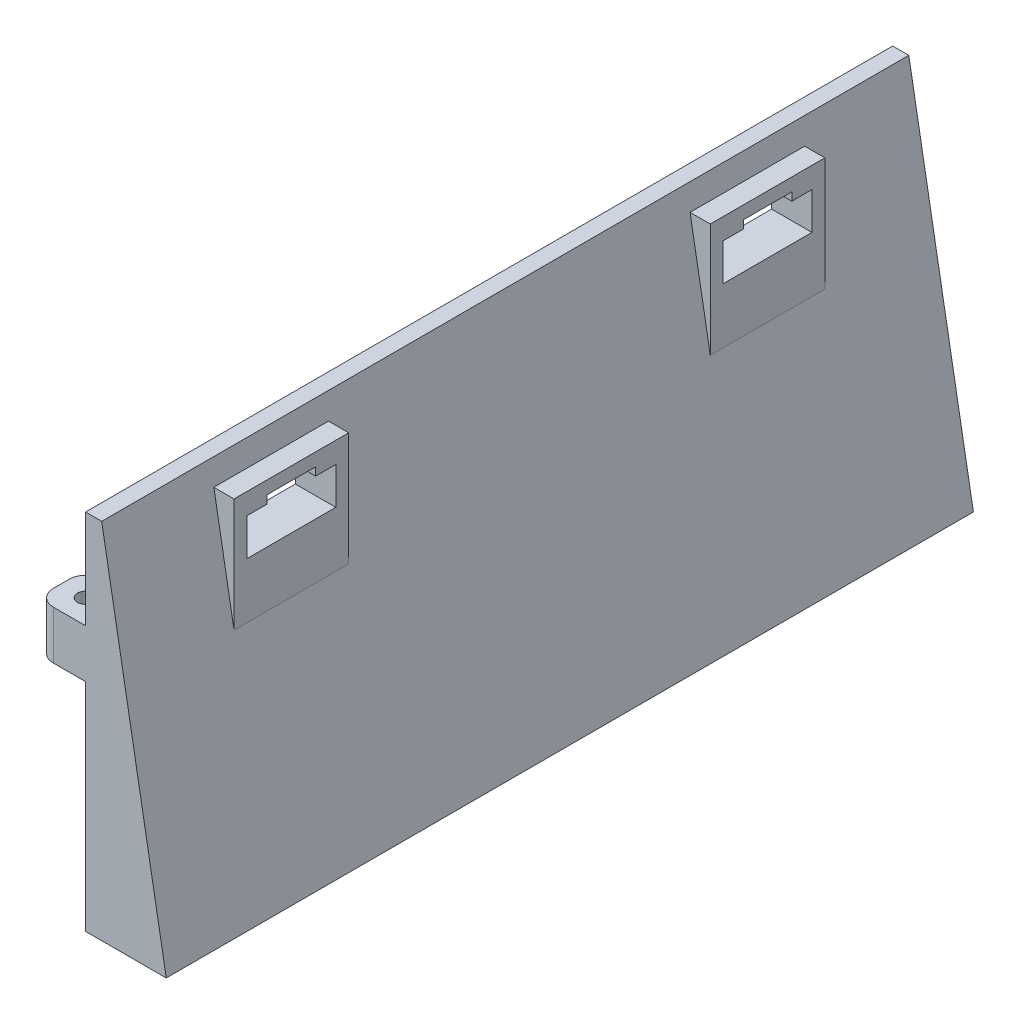
SolidWorks part; units mm, degrees
ref_plane "Front Plane" through (0, 0, 0) normal (0, 0, 1) x (1, 0, 0)
ref_plane "Top Plane" through (0, 0, 0) normal (0, 1, 0) x (1, 0, 0)
ref_plane "Right Plane" through (0, 0, 0) normal (1, 0, 0) x (0, 0, -1)
sketch "Sketch1" plane through (0, 0, 0) normal (0, 0, 1) x (1, 0, 0)
  line L0 (0, 0) -> (10, 0)
  line L1 (0, 0) -> (0, 45)
  line L2 (0, 45) -> (2, 45)
  line L3 (2, 45) -> (10, 0)
  dimension "D1" = 10
  dimension "D2" = 45
  dimension "D3" = 2
extrude "Boss-Extrude1" add sketch "Sketch1" along normal blind 100
sketch "Sketch3" plane through (0, 0, 0) normal (-1, 0, 0) x (0, 0, 1)
  line L0 (12.5, 0) -> (0, 0) construction
  line L1 (100, 0) -> (0, 0) construction
  line L2 (87.5, 0) -> (100, 0) construction
  line L3 (12.5, 0) -> (12.5, 7.1) construction
  line L4 (12.5, 7.1) -> (18.5, 7.1)
  line L5 (12.5, 7.1) -> (12.5, 13.1)
  line L6 (12.5, 13.1) -> (18.5, 13.1)
  line L7 (18.5, 13.1) -> (18.5, 7.1)
  line L8 (87.5, 0) -> (87.5, 7.1) construction
  line L9 (87.5, 7.1) -> (81.5, 7.1)
  line L10 (87.5, 7.1) -> (87.5, 13.1)
  line L11 (87.5, 13.1) -> (81.5, 13.1)
  line L12 (81.5, 13.1) -> (81.5, 7.1)
  line L13 (12.5, 7.1) -> (12.5, 13.1) construction
  dimension "D2" = 12.5
  dimension "D3" = 7.1
  dimension "D4" = 6
  dimension "D5" = 6
  dimension "D6" = 7.1
  dimension "D7" = 6
  dimension "D8" = 6
  dimension "D15" = 12.5
extrude "Boss-Extrude2" add sketch "Sketch3" along normal blind 6
sketch "Sketch4" plane through (0, 13.1, 0) normal (0, 1, 0) x (1, 0, 0)
  line L0 (-6, -84.5) -> (-3, -84.5) construction
  line L1 (-6, -87.5) -> (-6, -81.5) construction
  circle A0 centre (-3, -84.5) radius 1
  dimension "D2" = 2
  dimension "D1" = 3
extrude "Cut-Extrude2" cut sketch "Sketch4" against normal blind 10
sketch "Sketch5" plane through (0, 13.1, 0) normal (0, 1, 0) x (1, 0, 0)
  line L0 (-6, -15.5) -> (-3, -15.5) construction
  line L1 (-6, -18.5) -> (-6, -12.5) construction
  circle A0 centre (-3, -15.5) radius 1
  dimension "D2" = 2
  dimension "D1" = 3
extrude "Cut-Extrude3" cut sketch "Sketch5" against normal blind 10
fillet "Fillet1" radius 1 4 edges at (0, 10.1, 81.5) (0, 10.1, 87.5) (0, 10.1, 12.5) (0, 10.1, 18.5)
fillet "Fillet2" radius 2 4 edges at (-6, 10.1, 87.5) (-6, 10.1, 81.5) (-6, 10.1, 18.5) (-6, 10.1, 12.5)
sketch "Sketch7" plane through (0, 0, 0) normal (-1, 0, 0) x (0, 0, 1)
  line L0 (0, 45) -> (0, 40.6) construction
  line L1 (0, 45) -> (0, 0) construction
  line L2 (0, 40.6) -> (100, 40.6) construction
  line L3 (100, 45) -> (100, 0) construction
  line L4 (0, 40.6) -> (15, 40.6) construction
  line L5 (100, 40.6) -> (85, 40.6) construction
  line L6 (0, 40.6) -> (0, 35) construction
  line L7 (0, 35) -> (100, 35) construction
  line L8 (15, 40.6) -> (26, 40.6) construction
  line L9 (85, 40.6) -> (74, 40.6) construction
  line L10 (15, 40.6) -> (15, 35)
  line L11 (15, 35) -> (26, 35)
  line L12 (26, 35) -> (26, 40.6)
  line L13 (26, 40.6) -> (15, 40.6)
  line L14 (74, 40.6) -> (74, 35)
  line L15 (74, 35) -> (85, 35)
  line L16 (85, 35) -> (85, 40.6)
  line L17 (85, 40.6) -> (74, 40.6)
  dimension "D1" = 4.4
  dimension "D2" = 15
  dimension "D3" = 15
  dimension "D4" = 5.6
  dimension "D5" = 11
  dimension "D6" = 11
extrude "Cut-Extrude4" cut sketch "Sketch7" against normal blind 10
sketch "Sketch13" plane through (0, 0, 0) normal (-1, 0, 0) x (0, 0, 1)
  line L0 (11.5, 7.1) -> (11.5, 32.8) construction
  line L1 (11.5, 32.8) -> (0, 32.8) construction
  line L2 (0, 45) -> (0, 0) construction
  line L3 (11.5, 32.8) -> (100, 32.8) construction
  line L4 (100, 45) -> (100, 0) construction
  line L5 (0, 32.8) -> (0, 26.8)
  line L6 (0, 26.8) -> (100, 26.8) construction
  line L7 (0, 26.8) -> (6, 26.8)
  line L8 (6, 26.8) -> (6, 32.8)
  line L9 (6, 32.8) -> (0, 32.8)
  line L10 (100, 26.8) -> (100, 32.8)
  line L11 (100, 32.8) -> (94, 32.8)
  line L12 (94, 32.8) -> (94, 26.8)
  line L13 (94, 26.8) -> (100, 26.8)
  dimension "D1" = 25.7
  dimension "D2" = 6
  dimension "D3" = 6
  dimension "D4" = 6
extrude "Boss-Extrude3" add sketch "Sketch13" along normal blind 6
sketch "Sketch14" plane through (0, 32.8, 0) normal (0, 1, 0) x (1, 0, 0)
  line L0 (-6, -3) -> (-3, -3) construction
  line L1 (-6, -6) -> (-6, 0) construction
  circle A0 centre (-3, -3) radius 1
  dimension "D2" = 2
  dimension "D1" = 3
extrude "Cut-Extrude7" cut sketch "Sketch14" against normal blind 6
sketch "Sketch16" plane through (0, 32.8, 0) normal (0, 1, 0) x (1, 0, 0)
  line L0 (-6, -97) -> (-3, -97) construction
  line L1 (-6, -100) -> (-6, -94) construction
  circle A0 centre (-3, -97) radius 1
  dimension "D2" = 2
  dimension "D1" = 3
extrude "Cut-Extrude8" cut sketch "Sketch16" against normal blind 6
fillet "Fillet3" radius 2 4 edges at (-6, 29.8, 100) (-6, 29.8, 94) (-6, 29.8, 6) (-6, 29.8, 0)
fillet "Fillet4" radius 1 2 edges at (0, 29.8, 94) (0, 29.8, 6)
sketch "Sketch17" plane through (0, 0, 0) normal (-1, 0, 0) x (0, 0, 1)
  line L0 (15, 35) -> (13.4, 35)
  line L1 (15, 35) -> (15, 40.6)
  line L2 (26, 35) -> (27.6, 35)
  line L3 (15, 40.6) -> (15, 42.2) construction
  line L4 (15, 40.6) -> (26, 40.6)
  line L5 (26, 40.6) -> (26, 35)
  line L6 (13.4, 35) -> (13.4, 42.2)
  line L7 (13.4, 42.2) -> (15, 42.2)
  line L8 (15, 42.2) -> (27.6, 42.2)
  line L9 (27.6, 42.2) -> (27.6, 35)
  line L10 (74, 35) -> (72.4, 35)
  line L11 (85, 35) -> (86.6, 35)
  line L12 (74, 40.6) -> (74, 42.2) construction
  line L13 (74, 35) -> (74, 40.6)
  line L14 (74, 40.6) -> (85, 40.6)
  line L15 (85, 40.6) -> (85, 35)
  line L16 (72.4, 35) -> (72.4, 42.2)
  line L17 (72.4, 42.2) -> (74, 42.2)
  line L18 (74, 42.2) -> (86.6, 42.2)
  line L19 (86.6, 42.2) -> (86.6, 35)
  dimension "D1" = 1.6
  dimension "D2" = 1.6
  dimension "D3" = 1.6
  dimension "D4" = 1.6
  dimension "D5" = 1.6
  dimension "D6" = 1.6
extrude "Boss-Extrude4" add sketch "Sketch17" against normal blind 5
sketch "Sketch18" plane through (0, 0, 0) normal (-1, 0, 0) x (0, 0, 1)
  line L0 (15, 35) -> (13.4, 35)
  line L1 (13.4, 35) -> (13.4, 33.4)
  line L2 (26, 35) -> (27.6, 35)
  line L3 (13.4, 33.4) -> (27.6, 33.4)
  line L4 (27.6, 33.4) -> (27.6, 35)
  line L5 (15, 35) -> (26, 35)
  line L6 (74, 35) -> (72.4, 35)
  line L7 (85, 35) -> (86.6, 35)
  line L8 (72.4, 35) -> (72.4, 33.4)
  line L9 (72.4, 33.4) -> (86.6, 33.4)
  line L10 (86.6, 33.4) -> (86.6, 35)
  line L11 (74, 35) -> (85, 35)
  dimension "D1" = 1.6
  dimension "D2" = 1.6
  dimension "D3" = 1.6
  dimension "D4" = 1.6
  dimension "D5" = 1.6
  dimension "D6" = 1.6
extrude "Boss-Extrude5" add sketch "Sketch18" against normal blind 5
sketch "Sketch19" plane through (0, 33.4, 0) normal (0, -1, 0) x (1, 0, 0)
  line L0 (5, 86.6) -> (4.0622, 86.6)
  line L1 (4.0622, 86.6) -> (4.0622, 72.4)
  line L2 (4.0622, 72.4) -> (5, 72.4)
  line L3 (5, 72.4) -> (5, 86.6)
extrude "Boss-Extrude6" add sketch "Sketch19" along normal blind 10
sketch "Sketch20" plane through (0, 33.4, 0) normal (0, -1, 0) x (1, 0, 0)
  line L0 (4.0622, 27.6) -> (4.0622, 13.4)
  line L1 (4.0622, 13.4) -> (5, 13.4)
  line L2 (5, 13.4) -> (5, 27.6)
  line L3 (5, 27.6) -> (4.0622, 27.6)
extrude "Boss-Extrude7" add sketch "Sketch20" along normal blind 10
sketch "Sketch21" plane through (0, 40.6, 0) normal (0, -1, 0) x (1, 0, 0)
  line L0 (5, 85) -> (3, 85)
  line L1 (5, 85) -> (0, 85) construction
  line L2 (5, 85) -> (5, 82.5)
  line L3 (5, 74) -> (5, 85) construction
  line L4 (3, 85) -> (3, 82.5)
  line L5 (3, 82.5) -> (5, 82.5)
  line L6 (5, 74) -> (3, 74)
  line L7 (5, 74) -> (0, 74) construction
  line L8 (5, 74) -> (5, 76.5)
  line L9 (5, 76.5) -> (3, 76.5)
  line L10 (3, 76.5) -> (3, 74)
  dimension "D1" = 2
  dimension "D2" = 2.5
  dimension "D3" = 2
  dimension "D4" = 2.5
extrude "Boss-Extrude8" add sketch "Sketch21" along normal blind 1
sketch "Sketch22" plane through (0, 40.6, 0) normal (0, -1, 0) x (1, 0, 0)
  line L0 (5, 15) -> (3, 15)
  line L1 (5, 15) -> (0, 15) construction
  line L2 (5, 15) -> (5, 17.5)
  line L3 (5, 15) -> (5, 26) construction
  line L4 (5, 17.5) -> (3, 17.5)
  line L5 (3, 17.5) -> (3, 15)
  line L6 (5, 26) -> (3, 26)
  line L7 (5, 26) -> (0, 26) construction
  line L8 (5, 26) -> (5, 23.5)
  line L9 (3, 26) -> (3, 23.5)
  line L10 (3, 23.5) -> (5, 23.5)
  dimension "D1" = 2
  dimension "D2" = 2.5
  dimension "D3" = 2
  dimension "D4" = 2.5
extrude "Boss-Extrude9" add sketch "Sketch22" along normal blind 1
